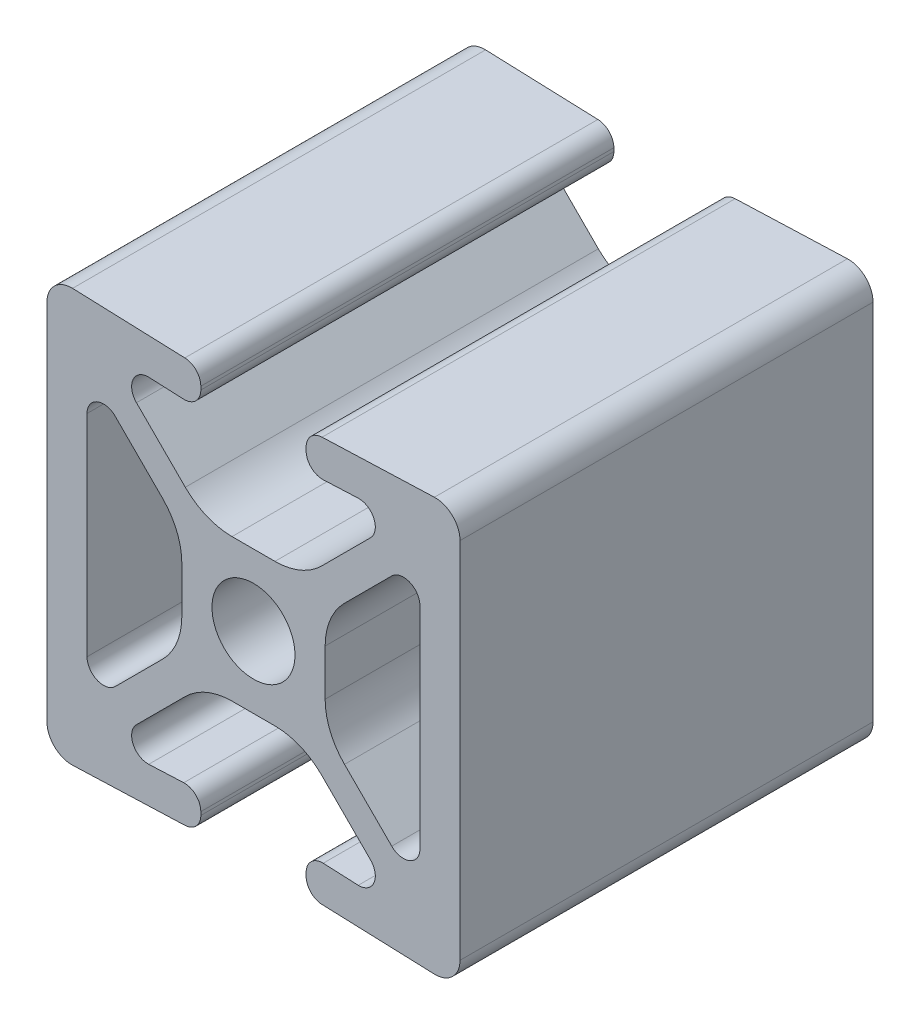
SolidWorks part; units mm, degrees
material "6061 Alloy"
ref_plane "Front" through (0, 0, 0) normal (0, 0, 1) x (1, 0, 0)
ref_plane "Top" through (0, 0, 0) normal (0, 1, 0) x (1, 0, 0)
ref_plane "Right" through (0, 0, 0) normal (1, 0, 0) x (0, 0, -1)
sketch "Sketch1" plane through (0, 0, 0) normal (0, 0, 1) x (1, 0, 0)
  line L0 (-8.5018, 7.1954) -> (-5.5972, 4.2909)
  line L1 (-10.2362, 0) -> (-10.2362, 6.477)
  line L2 (-4.4069, -1.4172) -> (-4.4069, 1.4172)
  line L3 (-10.2362, 0) -> (-10.2362, -6.477)
  line L4 (-8.5018, -7.1954) -> (-5.5972, -4.2909)
  line L5 (10.2362, 0) -> (10.2362, 6.477)
  line L6 (10.2362, 0) -> (10.2362, -6.477)
  line L7 (8.5018, 7.1954) -> (5.5972, 4.2909)
  line L8 (8.5018, -7.1954) -> (5.5972, -4.2909)
  line L9 (4.4069, -1.4172) -> (4.4069, 1.4172)
  line L10 (11.1257, 12.6992) -> (4.221, 12.4456)
  line L11 (12.7, 0) -> (12.7, 11.176)
  line L12 (12.7, 0) -> (12.7, -11.176)
  line L13 (3.2385, 11.2269) -> (3.2385, 11.4302)
  line L14 (11.1257, -12.6992) -> (4.221, -12.4456)
  line L15 (6.4435, 10.3081) -> (4.288, 10.2114)
  line L16 (3.2385, -11.2269) -> (3.2385, -11.4302)
  line L17 (7.1954, 8.5742) -> (4.1931, 5.5718)
  line L18 (6.4435, -10.3081) -> (4.288, -10.2114)
  line L19 (1.3194, 4.3815) -> (-1.3194, 4.3815)
  line L20 (7.1954, -8.5742) -> (4.1931, -5.5718)
  line L21 (-7.1954, 8.5742) -> (-4.1931, 5.5718)
  line L22 (1.3194, -4.3815) -> (-1.3194, -4.3815)
  line L23 (-6.4435, 10.3081) -> (-4.288, 10.2114)
  line L24 (-7.1954, -8.5742) -> (-4.1931, -5.5718)
  line L25 (-3.2385, 11.2269) -> (-3.2385, 11.4302)
  line L26 (-6.4435, -10.3081) -> (-4.288, -10.2114)
  line L27 (-11.1257, 12.6992) -> (-4.221, 12.4456)
  line L28 (-3.2385, -11.2269) -> (-3.2385, -11.4302)
  line L29 (-12.7, 0) -> (-12.7, 11.176)
  line L30 (-12.7, 0) -> (-12.7, -11.176)
  line L31 (-11.1257, -12.6992) -> (-4.221, -12.4456)
  arc A0 (-8.5018, 7.1954) -> (-10.2362, 6.477) centre (-9.2202, 6.477) ccw
  arc A1 (-4.4069, 1.4172) -> (-5.5972, 4.2909) centre (-8.4709, 1.4172) ccw
  arc A2 (-5.5972, -4.2909) -> (-4.4069, -1.4172) centre (-8.4709, -1.4172) ccw
  arc A3 (-10.2362, -6.477) -> (-8.5018, -7.1954) centre (-9.2202, -6.477) ccw
  arc A4 (10.2362, 6.477) -> (8.5018, 7.1954) centre (9.2202, 6.477) ccw
  arc A5 (8.5018, -7.1954) -> (10.2362, -6.477) centre (9.2202, -6.477) ccw
  arc A6 (5.5972, 4.2909) -> (4.4069, 1.4172) centre (8.4709, 1.4172) ccw
  arc A7 (4.4069, -1.4172) -> (5.5972, -4.2909) centre (8.4709, -1.4172) ccw
  arc A8 (12.7, 11.176) -> (11.1257, 12.6992) centre (11.176, 11.176) ccw
  arc A9 (4.221, 12.4456) -> (3.2385, 11.4302) centre (4.2545, 11.4302) ccw
  arc A10 (11.1257, -12.6992) -> (12.7, -11.176) centre (11.176, -11.176) ccw
  arc A11 (3.2385, 11.2269) -> (4.288, 10.2114) centre (4.2545, 11.2269) ccw
  arc A12 (3.2385, -11.4302) -> (4.221, -12.4456) centre (4.2545, -11.4302) ccw
  arc A13 (7.1954, 8.5742) -> (6.4435, 10.3081) centre (6.477, 9.2926) ccw
  arc A14 (4.288, -10.2114) -> (3.2385, -11.2269) centre (4.2545, -11.2269) ccw
  arc A15 (1.3194, 4.3815) -> (4.1931, 5.5718) centre (1.3194, 8.4455) ccw
  arc A16 (6.4435, -10.3081) -> (7.1954, -8.5742) centre (6.477, -9.2926) ccw
  arc A17 (-4.1931, 5.5718) -> (-1.3194, 4.3815) centre (-1.3194, 8.4455) ccw
  arc A18 (4.1931, -5.5718) -> (1.3194, -4.3815) centre (1.3194, -8.4455) ccw
  arc A19 (-6.4435, 10.3081) -> (-7.1954, 8.5742) centre (-6.477, 9.2926) ccw
  arc A20 (-1.3194, -4.3815) -> (-4.1931, -5.5718) centre (-1.3194, -8.4455) ccw
  arc A21 (-4.288, 10.2114) -> (-3.2385, 11.2269) centre (-4.2545, 11.2269) ccw
  arc A22 (-7.1954, -8.5742) -> (-6.4435, -10.3081) centre (-6.477, -9.2926) ccw
  arc A23 (-3.2385, 11.4302) -> (-4.221, 12.4456) centre (-4.2545, 11.4302) ccw
  arc A24 (-3.2385, -11.2269) -> (-4.288, -10.2114) centre (-4.2545, -11.2269) ccw
  arc A25 (-11.1257, 12.6992) -> (-12.7, 11.176) centre (-11.176, 11.176) ccw
  arc A26 (-4.221, -12.4456) -> (-3.2385, -11.4302) centre (-4.2545, -11.4302) ccw
  arc A27 (-12.7, -11.176) -> (-11.1257, -12.6992) centre (-11.176, -11.176) ccw
  arc A28 (0, 2.5527) -> (-2.5527, 0) centre (0, 0) ccw
  arc A29 (-2.5527, 0) -> (0, -2.5527) centre (0, 0) ccw
  arc A30 (2.5527, 0) -> (0, 2.5527) centre (0, 0) ccw
  arc A31 (0, -2.5527) -> (2.5527, 0) centre (0, 0) ccw
extrude "Extrude1" add sketch "Sketch1" along normal blind 25.4
